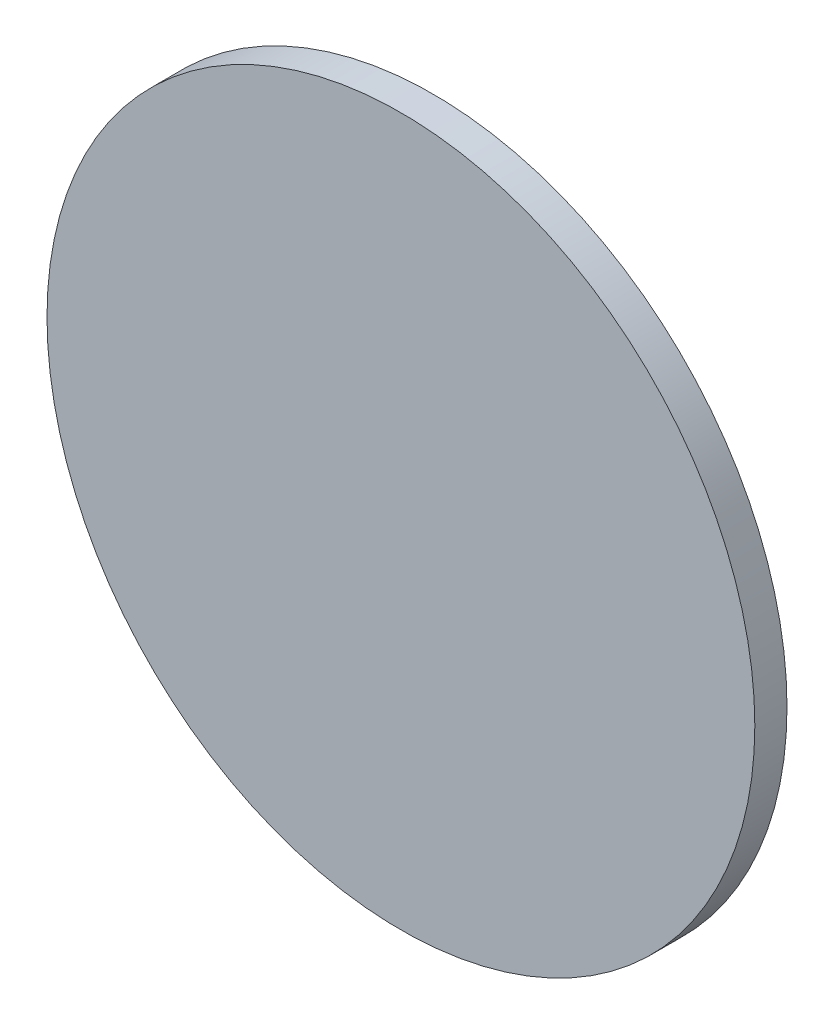
SolidWorks part; units mm, degrees
ref_plane "Front Plane" through (0, 0, 0) normal (0, 0, 1) x (1, 0, 0)
ref_plane "Top Plane" through (0, 0, 0) normal (0, 1, 0) x (1, 0, 0)
ref_plane "Right Plane" through (0, 0, 0) normal (1, 0, 0) x (0, 0, -1)
sketch "Sketch1" plane through (0, 0, 0) normal (0, 0, 1) x (1, 0, 0)
  line L5 (-12.7, -139.7) -> (12.7, -139.7)
  line L6 (-12.7, -139.7) -> (-12.7, 139.7)
  line L7 (-12.7, 139.7) -> (12.7, 139.7)
  line L8 (12.7, -139.7) -> (12.7, 139.7)
  line L9 (-12.7, -139.7) -> (12.7, 139.7) construction
  line L10 (-12.7, 139.7) -> (12.7, -139.7) construction
  point P0 (0, 0)
  dimension "D1" = 25.4
  dimension "D2" = 279.4
extrude "Boss-Extrude1" [suppressed] add sketch "Sketch1" against normal blind 12.7
sketch "Sketch2" plane through (0, 0, 0) normal (0, 0, 1) x (1, 0, 0)
  circle A0 centre (0, 0) radius 139.7
  dimension "D1" = 279.4
extrude "Boss-Extrude3" add sketch "Sketch2" against normal blind 12.7
